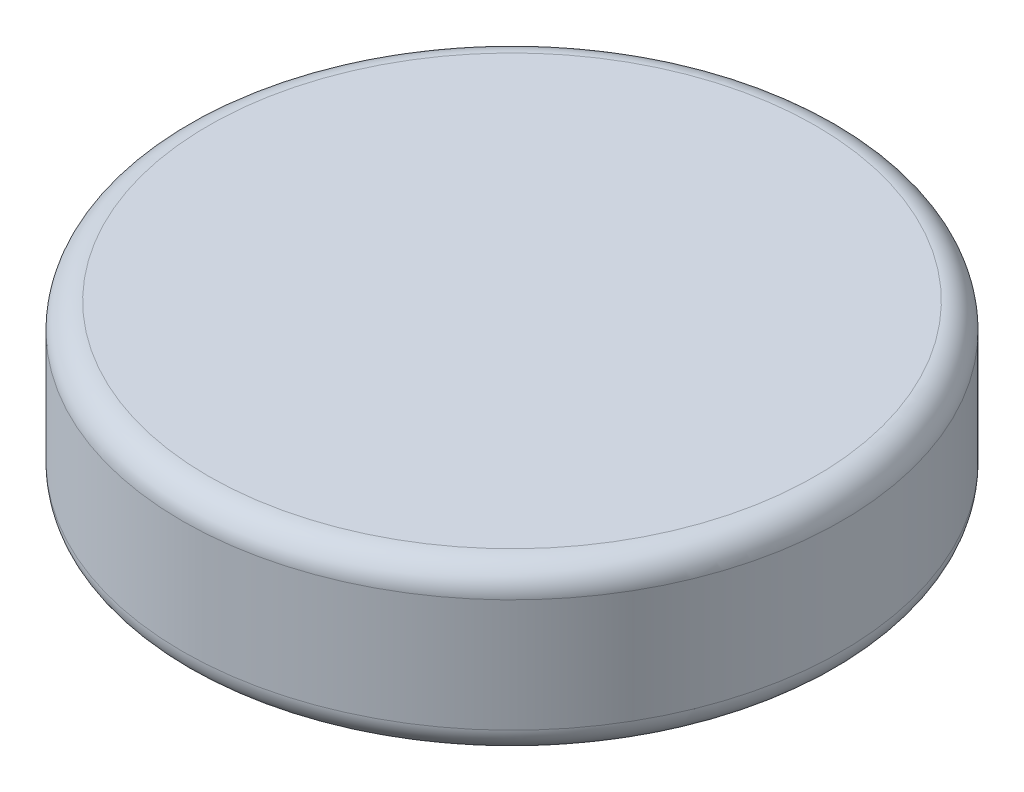
SolidWorks part; units mm, degrees
material "Chrome Stainless Steel"
ref_plane "Front Plane" through (0, 0, 0) normal (0, 0, 1) x (1, 0, 0)
ref_plane "Top Plane" through (0, 0, 0) normal (0, 1, 0) x (1, 0, 0)
ref_plane "Right Plane" through (0, 0, 0) normal (1, 0, 0) x (0, 0, -1)
sketch "Sketch2" plane through (0, 0, 0) normal (0, 1, 0) x (1, 0, 0)
  circle A0 centre (0, 0) radius 3.175
  dimension "D1" = 6.35
extrude "Boss-Extrude1" add sketch "Sketch2" along normal blind 1.5875
fillet "Fillet1" radius 0.25 2 edges at (0, 0, 3.175) (0, 1.5875, 3.175)
